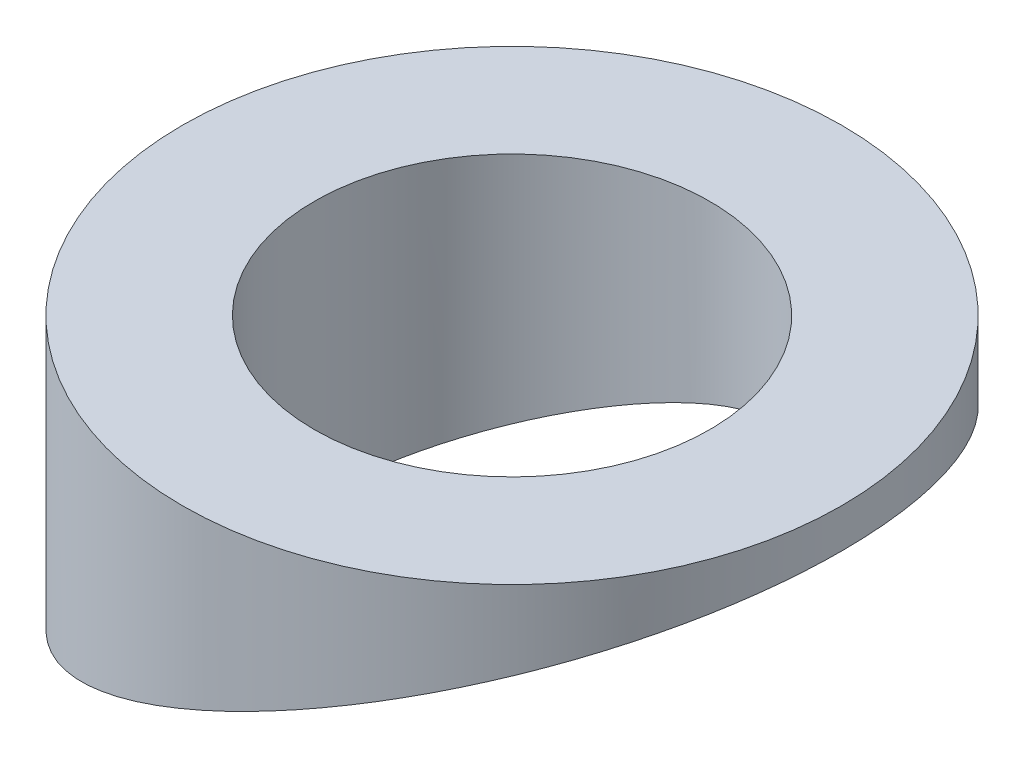
SolidWorks part; units mm, degrees
ref_plane "前视基准面" through (0, 0, 0) normal (0, 0, 1) x (1, 0, 0)
ref_plane "上视基准面" through (0, 0, 0) normal (0, 1, 0) x (1, 0, 0)
ref_plane "右视基准面" through (0, 0, 0) normal (1, 0, 0) x (0, 0, -1)
sketch "草图1" plane through (0, 0, 0) normal (0, 1, 0) x (1, 0, 0)
  circle A0 centre (0, 0) radius 15
  dimension "D1" = 30
extrude "凸台-拉伸1" add sketch "草图1" along normal blind 20
sketch "草图2" plane through (0, 0, 0) normal (0, 0, 1) x (1, 0, 0)
  line L0 (-15, 5.7868) -> (15, 18.2132)
  line L1 (15, 18.2132) -> (15, -10.3775)
  line L2 (15, -10.3775) -> (-15, -10.3775)
  line L3 (-15, -10.3775) -> (-15, 5.7868)
  line L4 (0, -10.3775) -> (0, 12) construction
  line L5 (-15, 0) -> (15, 0) construction
  dimension "D1" = 30
  dimension "D2" = 0
  dimension "D3" = 12
  dimension "D4" = 22.5
extrude "切除-拉伸1" cut sketch "草图2" against normal mid plane 33
ref_point "点1"
sketch "草图4" plane through (-4.2426, 10.2426, 0) normal (0.3827, -0.9239, 0) x (-0.9239, -0.3827, 0)
  line L0 (11.6437, 0) -> (-20.8281, 0) construction
  line L1 (-4.5922, -15) -> (-4.5922, 15) construction
  ellipse E0 centre (-4.5922, 0) end of major axis (11.6437, 0) minor radius 15 construction
sketch "草图6" plane through (0, 20, 0) normal (0, 1, 0) x (1, 0, 0)
  line L0 (-15, 0) -> (15, 0) construction
  line L1 (0, -15) -> (0, 15) construction
  circle A0 centre (0, 0) radius 15 construction
sketch "草图7" plane through (0, 0, 0) normal (0, 0, 1) x (1, 0, 0)
  line L0 (0, 20) -> (0, 12)
  line L1 (-15, 20) -> (15, 20) construction
  line L2 (-15, 5.7868) -> (15, 18.2132) construction
sketch "草图8" plane through (0, 0, 0) normal (0, 0, 1) x (1, 0, 0)
  line L0 (-15, 20) -> (-15, 5.7868) construction
  line L1 (15, 20) -> (15, 18.2132) construction
sketch "草图9" plane through (0, 0, 0) normal (1, 0, 0) x (0, 0, -1)
  line L0 (-15, 20) -> (-15, 12) construction
  line L1 (15, 20) -> (15, 12) construction
sketch "草图10" plane through (0, 20, 0) normal (0, 1, 0) x (1, 0, 0)
  circle A0 centre (0, 0) radius 9
  dimension "D1" = 18
extrude "切除-拉伸2" cut sketch "草图10" against normal blind 24.5
